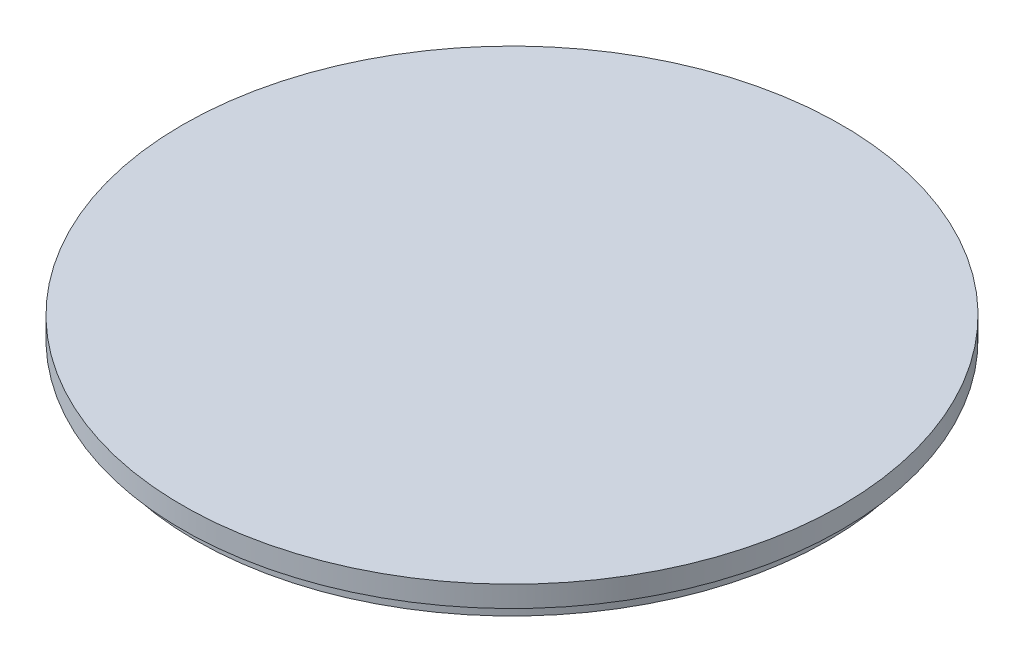
SolidWorks part; units mm, degrees
ref_plane "Front Plane" through (0, 0, 0) normal (0, 0, 1) x (1, 0, 0)
ref_plane "Top Plane" through (0, 0, 0) normal (0, 1, 0) x (1, 0, 0)
ref_plane "Right Plane" through (0, 0, 0) normal (1, 0, 0) x (0, 0, -1)
sketch "Sketch1" plane through (0, 0, 0) normal (0, 0, 1) x (1, 0, 0)
  line L0 (0, 0) -> (0, 4)
  line L1 (0, 4) -> (-62.5, 4)
  line L2 (-62.5, 4) -> (-62.5, 0)
  line L3 (-62.5, 0) -> (-60, 0)
  line L4 (-60, 0) -> (-60, -3)
  line L5 (-60, -3) -> (-58.2679, 0)
  line L6 (-58.2679, 0) -> (0, 0)
  dimension "D1" = 62.5
  dimension "D2" = 4
  dimension "D3" = 3
  dimension "D4" = 60
  dimension "D5" = 30
revolve "Revolve1" add sketch "Sketch1" angle 360 about L0
